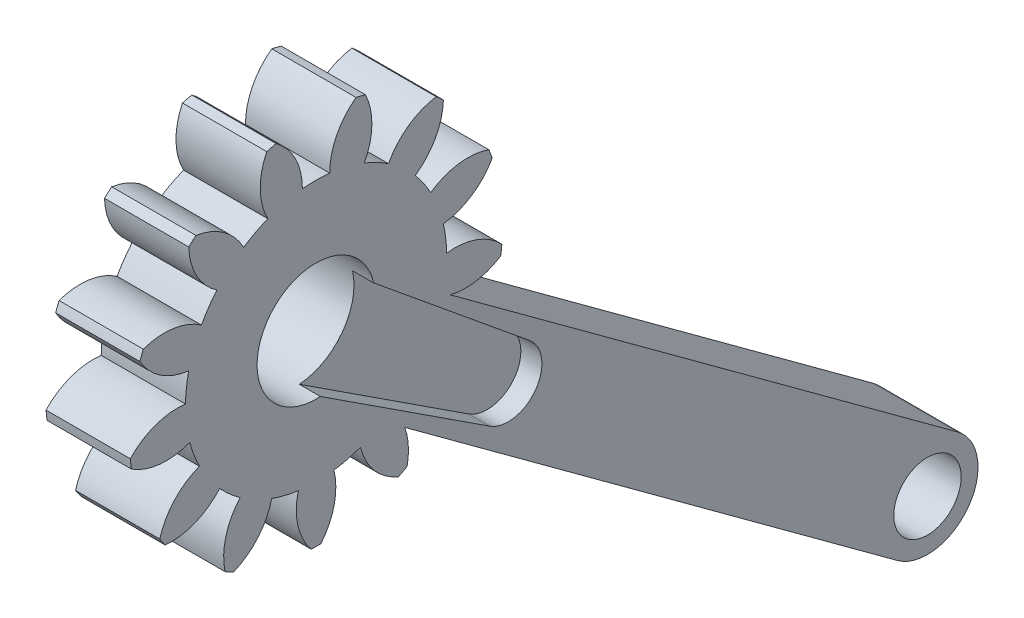
SolidWorks part; units mm, degrees
ref_plane "Front Plane" through (0, 0, 0) normal (0, 0, 1) x (1, 0, 0)
ref_plane "Top Plane" through (0, 0, 0) normal (0, 1, 0) x (1, 0, 0)
ref_plane "Right Plane" through (0, 0, 0) normal (1, 0, 0) x (0, 0, -1)
ref_plane "Plane1" through (-2.7128, 0, 0) normal (1, 0, 0) x (0, 0, -1)
sketch "Sketch1" plane through (-2.7128, 0, 0) normal (1, 0, 0) x (0, 0, -1)
  circle A0 centre (-74.3928, 33.7527) radius 3.5
  arc A1 (-81.9478, 41.8497) -> (-80.2755, 38.7992) centre (-78.1106, 41.9696) ccw
  arc A2 (-80.2755, 38.7992) -> (-81.1974, 37.4636) centre (-74.3928, 33.7527) ccw
  arc A3 (-81.1974, 37.4636) -> (-84.6427, 37.9455) centre (-83.3941, 34.3151) ccw
  arc A4 (-84.6427, 37.9455) -> (-84.8453, 37.4113) centre (-74.3928, 33.7527) ccw
  arc A5 (-84.8453, 37.4113) -> (-81.9469, 35.4873) centre (-81.5034, 39.3007) ccw
  arc A6 (-81.9469, 35.4873) -> (-82.1425, 33.8763) centre (-74.3928, 33.7527) ccw
  arc A7 (-82.1425, 33.8763) -> (-85.4171, 32.7019) centre (-82.6245, 30.0676) ccw
  arc A8 (-85.4171, 32.7019) -> (-85.3482, 32.1347) centre (-74.3928, 33.7527) ccw
  arc A9 (-85.3482, 32.1347) -> (-81.8877, 31.7781) centre (-83.2672, 35.3608) ccw
  arc A10 (-81.8877, 31.7781) -> (-81.3123, 30.2607) centre (-74.3928, 33.7527) ccw
  arc A11 (-81.3123, 30.2607) -> (-83.666, 27.6991) centre (-79.969, 26.6643) ccw
  arc A12 (-83.666, 27.6991) -> (-83.3414, 27.2288) centre (-74.3928, 33.7527) ccw
  arc A13 (-83.3414, 27.2288) -> (-80.1116, 28.5212) centre (-82.998, 31.0525) ccw
  arc A14 (-80.1116, 28.5212) -> (-78.8969, 27.4451) centre (-74.3928, 33.7527) ccw
  arc A15 (-78.8969, 27.4451) -> (-79.7905, 24.083) centre (-76.0362, 24.8848) ccw
  arc A16 (-79.7905, 24.083) -> (-79.2846, 23.8175) centre (-74.3928, 33.7527) ccw
  arc A17 (-79.2846, 23.8175) -> (-77.0254, 26.4628) centre (-80.7575, 27.3628) ccw
  arc A18 (-77.0254, 26.4628) -> (-75.4496, 26.0745) centre (-74.3928, 33.7527) ccw
  arc A19 (-75.4496, 26.0745) -> (-74.6785, 22.6822) centre (-71.7268, 25.1369) ccw
  arc A20 (-74.6785, 22.6822) -> (-74.1072, 22.6822) centre (-74.3928, 33.7527) ccw
  arc A21 (-74.1072, 22.6822) -> (-73.3361, 26.0745) centre (-77.0589, 25.1369) ccw
  arc A22 (-73.3361, 26.0745) -> (-71.7603, 26.4628) centre (-74.3928, 33.7527) ccw
  arc A23 (-71.7603, 26.4628) -> (-69.5011, 23.8175) centre (-68.0282, 27.3628) ccw
  arc A24 (-69.5011, 23.8175) -> (-68.9951, 24.083) centre (-74.3928, 33.7527) ccw
  arc A25 (-68.9951, 24.083) -> (-69.8888, 27.4451) centre (-72.7495, 24.8848) ccw
  arc A26 (-69.8888, 27.4451) -> (-68.6741, 28.5212) centre (-74.3928, 33.7527) ccw
  arc A27 (-68.6741, 28.5212) -> (-65.4443, 27.2288) centre (-65.7877, 31.0525) ccw
  arc A28 (-65.4443, 27.2288) -> (-65.1197, 27.6991) centre (-74.3928, 33.7527) ccw
  arc A29 (-65.1197, 27.6991) -> (-67.4734, 30.2607) centre (-68.8167, 26.6643) ccw
  arc A30 (-67.4734, 30.2607) -> (-66.898, 31.7781) centre (-74.3928, 33.7527) ccw
  arc A31 (-66.898, 31.7781) -> (-63.4375, 32.1347) centre (-65.5185, 35.3608) ccw
  arc A32 (-63.4375, 32.1347) -> (-63.3686, 32.7019) centre (-74.3928, 33.7527) ccw
  arc A33 (-63.3686, 32.7019) -> (-66.6432, 33.8763) centre (-66.1612, 30.0676) ccw
  arc A34 (-66.6432, 33.8763) -> (-66.8388, 35.4873) centre (-74.3928, 33.7527) ccw
  arc A35 (-66.8388, 35.4873) -> (-63.9404, 37.4113) centre (-67.2823, 39.3007) ccw
  arc A36 (-63.9404, 37.4113) -> (-64.143, 37.9455) centre (-74.3928, 33.7527) ccw
  arc A37 (-64.143, 37.9455) -> (-67.5883, 37.4636) centre (-65.3916, 34.3151) ccw
  arc A38 (-67.5883, 37.4636) -> (-68.5102, 38.7992) centre (-74.3928, 33.7527) ccw
  arc A39 (-68.5102, 38.7992) -> (-66.8379, 41.8497) centre (-70.6751, 41.9696) ccw
  arc A40 (-66.8379, 41.8497) -> (-67.2656, 42.2286) centre (-74.3928, 33.7527) ccw
  arc A41 (-67.2656, 42.2286) -> (-70.0922, 40.2008) centre (-66.684, 38.4338) ccw
  arc A42 (-70.0922, 40.2008) -> (-71.5292, 40.9549) centre (-74.3928, 33.7527) ccw
  arc A43 (-71.5292, 40.9549) -> (-71.4661, 44.4332) centre (-74.9195, 42.7562) ccw
  arc A44 (-71.4661, 44.4332) -> (-72.0209, 44.5699) centre (-74.3928, 33.7527) ccw
  arc A45 (-72.0209, 44.5699) -> (-73.5814, 41.4608) centre (-69.7424, 41.4801) ccw
  arc A46 (-73.5814, 41.4608) -> (-75.2043, 41.4608) centre (-74.3928, 33.7527) ccw
  arc A47 (-75.2043, 41.4608) -> (-76.7648, 44.5699) centre (-79.0433, 41.4801) ccw
  arc A48 (-76.7648, 44.5699) -> (-77.3196, 44.4332) centre (-74.3928, 33.7527) ccw
  arc A49 (-77.3196, 44.4332) -> (-77.2565, 40.9549) centre (-73.8662, 42.7562) ccw
  arc A50 (-77.2565, 40.9549) -> (-78.6935, 40.2008) centre (-74.3928, 33.7527) ccw
  arc A51 (-78.6935, 40.2008) -> (-81.5201, 42.2286) centre (-82.1017, 38.4338) ccw
  arc A52 (-81.5201, 42.2286) -> (-81.9478, 41.8497) centre (-74.3928, 33.7527) ccw
  dimension "D1" = 7
extrude "Boss-Extrude1" add sketch "Sketch1" against normal blind 5
sketch "Sketch2" plane through (-2.7128, 0, 0) normal (1, 0, 0) x (0, 0, -1)
  line L0 (-74.3928, 33.7527) -> (-38.1159, 7.126) construction
  line L1 (-72.6177, 36.1712) -> (-36.3408, 9.5444) construction
  line L2 (-76.168, 31.3342) -> (-39.891, 4.7075) construction
  line L3 (-72.6177, 36.1712) -> (-36.3408, 9.5444)
  line L4 (-76.168, 31.3342) -> (-39.891, 4.7075)
  arc A0 (-72.6177, 36.1712) -> (-76.168, 31.3342) centre (-74.3928, 33.7527) ccw construction
  arc A1 (-39.891, 4.7075) -> (-36.3408, 9.5444) centre (-38.1159, 7.126) ccw construction
  circle A2 centre (-38.1159, 7.126) radius 2
  circle A3 centre (-74.3928, 33.7527) radius 3.5 construction
  arc A5 (-36.3408, 9.5444) -> (-39.891, 4.7075) centre (-38.1159, 7.126) cw
  arc A6 (-74.7146, 30.2675) -> (-71.1644, 35.1045) centre (-74.3042, 33.6876) ccw
  point P2 (-56.2544, 20.4393)
  point P10 (-71.1644, 35.1045)
  point P11 (-74.7146, 30.2675)
  dimension "D2" = 4
  dimension "D1" = 6
  dimension "D3" = 45
extrude "Boss-Extrude2" add sketch "Sketch2" against normal blind 5 contours A6 L4 A5 L3 A2
sketch "Sketch4" plane through (-2.7128, 0, 0) normal (1, 0, 0) x (0, 0, -1)
  line L4 (-74.3928, 33.7527) -> (-38.1159, 7.126) construction
  line L5 (-0.129, 6.931) -> (-4.5425, -4.1934)
  line L6 (-4.5425, -4.1934) -> (-0.9158, -5.8667)
  line L7 (-0.9158, -5.8667) -> (4.6834, 4.7106)
  line L8 (-74.137, 30.2621) -> (-64.0842, 23.7092)
  line L9 (-64.0842, 23.7092) -> (-61.7238, 26.9312)
  line L10 (-61.7238, 26.9312) -> (-70.978, 34.52)
  arc A6 (-4.5425, -4.1934) -> (-0.9158, -5.8667) centre (-2.6834, -4.931) ccw
  arc A7 (-64.0842, 23.7092) -> (-61.7238, 26.9312) centre (-62.992, 25.3847) ccw
  circle A8 centre (-74.3928, 33.7527) radius 3.5 construction
  arc A9 (-74.137, 30.2621) -> (-70.978, 34.52) centre (-74.3928, 33.7527) ccw
  point P1 (0, 0)
  point P5 (0, 0)
  dimension "D6" = 2
  dimension "D3" = 11.9679
  dimension "D4" = 12
  dimension "D5" = 5.3018
extrude "Cut-Extrude1" cut sketch "Sketch4" against normal blind 1.25 contours L4 A9 L8 L9 | A9 L4 L9 L10 | L9 L4 A7 | L4 L9 A7
